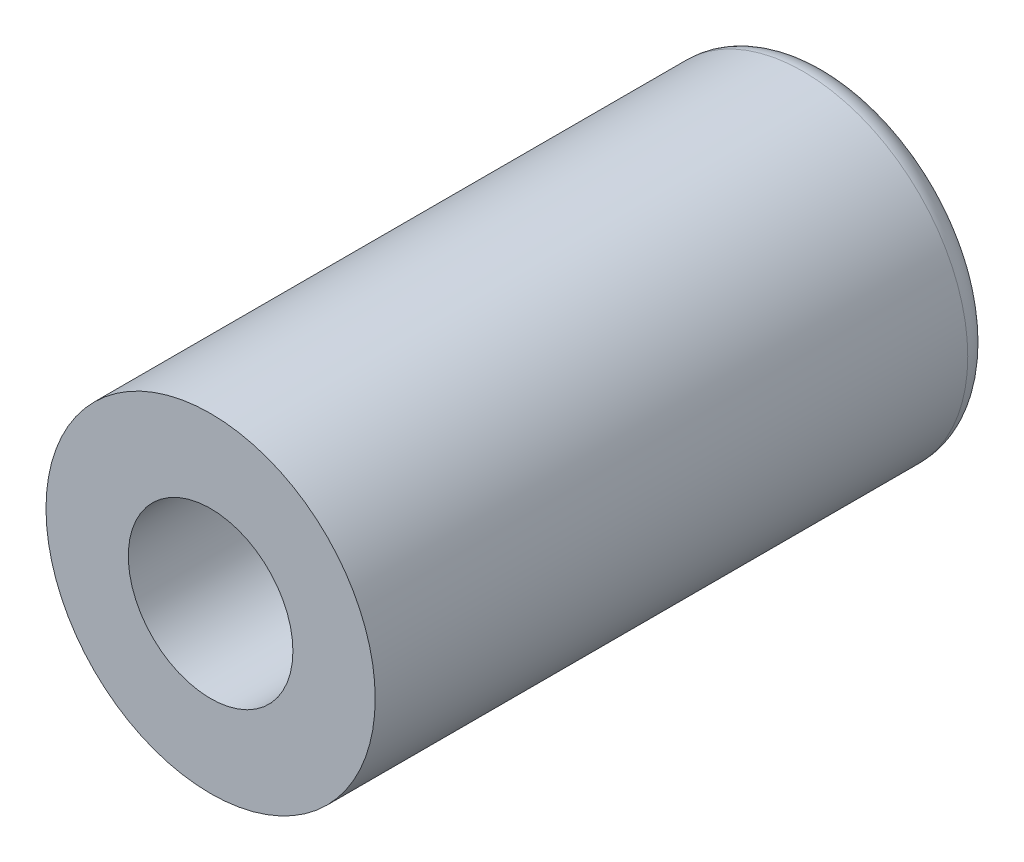
SolidWorks part; units mm, degrees
ref_plane "Front Plane" through (0, 0, 0) normal (0, 0, 1) x (1, 0, 0)
ref_plane "Top Plane" through (0, 0, 0) normal (0, 1, 0) x (1, 0, 0)
ref_plane "Right Plane" through (0, 0, 0) normal (1, 0, 0) x (0, 0, -1)
sketch "Sketch1" plane through (0, 0, 0) normal (0, 0, 1) x (1, 0, 0)
  circle A0 centre (0, 0) radius 4
  dimension "D1" = 8
extrude "Boss-Extrude1" add sketch "Sketch1" along normal blind 15
sketch "Sketch2" plane through (0, 0, 15) normal (0, 0, 1) x (1, 0, 0)
  circle A0 centre (0, 0) radius 2
  circle A1 centre (0, 0) radius 4 construction
  dimension "D1" = 2
extrude "Cut-Extrude1" cut sketch "Sketch2" against normal offset from surface (13 mm away) 2 up to face at (4, 0, 0)
fillet "Fillet1" radius 0.6 1 edges at (4, 0, 0)
